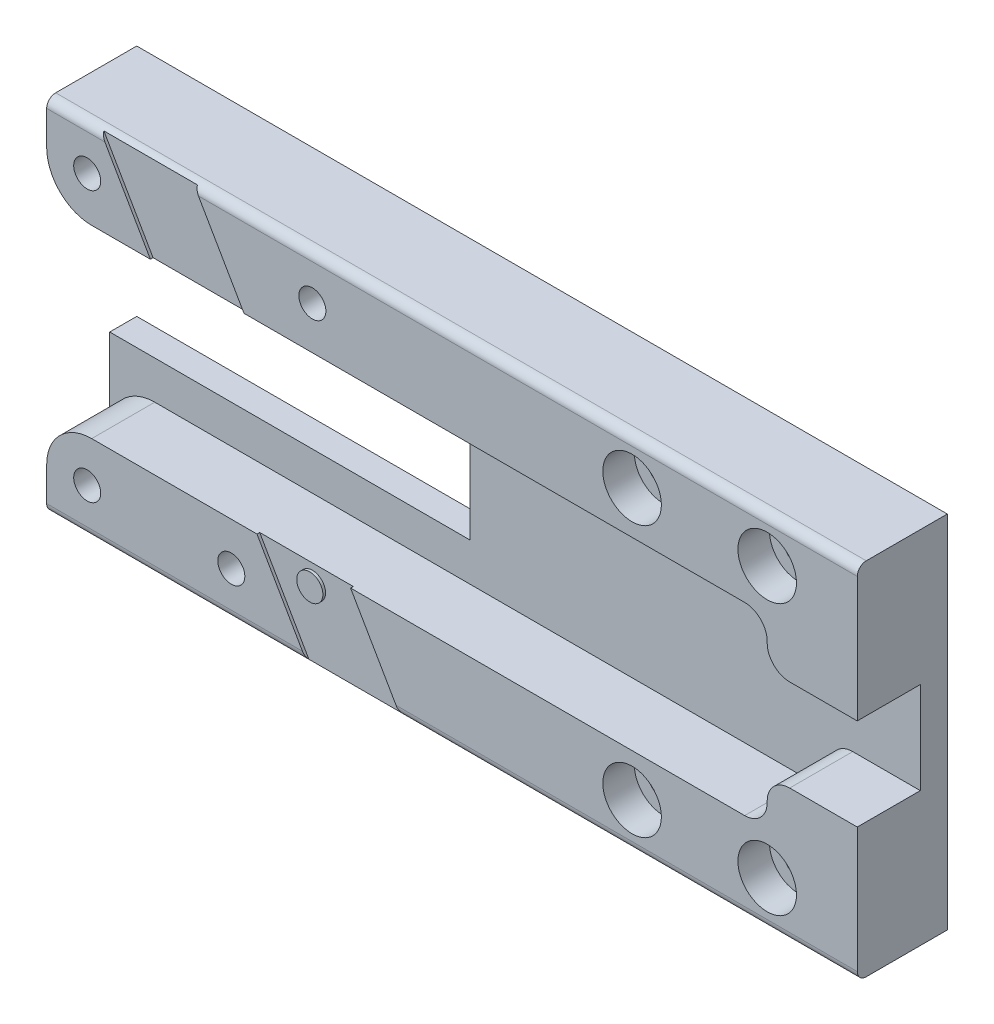
SolidWorks part; units mm, degrees
ref_plane "前视基准面" through (0, 0, 0) normal (0, 0, 1) x (1, 0, 0)
ref_plane "上视基准面" through (0, 0, 0) normal (0, 1, 0) x (1, 0, 0)
ref_plane "右视基准面" through (0, 0, 0) normal (1, 0, 0) x (0, 0, -1)
sketch "草图1" plane through (0, 0, 0) normal (0, 0, 1) x (1, 0, 0)
  line L1 (127.5, -40) -> (-127.5, -40)
  line L2 (127.5, -40) -> (127.5, 40)
  line L3 (127.5, 40) -> (-127.5, 40)
  line L4 (-127.5, -40) -> (-127.5, 40)
  line L5 (127.5, -40) -> (-127.5, 40) construction
  line L6 (127.5, 40) -> (-127.5, -40) construction
  point P0 (0, 0)
  dimension "D1" = 80
  dimension "D2" = 255
extrude "凸台-拉伸1" add sketch "草图1" along normal blind 5
sketch "草图2" plane through (0, 0, 5) normal (0, 0, 1) x (1, 0, 0)
  line L0 (-127.5, 40) -> (-127.5, -40) construction
  circle A0 centre (-107.5, 0) radius 5
  dimension "D1" = 10
  dimension "D2" = 20
extrude "切除-拉伸1" cut sketch "草图2" against normal blind 5
sketch "草图3" plane through (0, 0, 5) normal (0, 0, 1) x (1, 0, 0)
  circle A0 centre (-45, 0) radius 4
  dimension "D2" = 8
extrude "切除-拉伸2" cut sketch "草图3" against normal blind 10
sketch "草图4" plane through (0, 0, 5) normal (0, 0, 1) x (1, 0, 0)
  line L1 (2.5, -10) -> (-47.5, -10)
  line L2 (2.5, -10) -> (2.5, 10)
  line L3 (2.5, 10) -> (-47.5, 10)
  line L4 (-47.5, -10) -> (-47.5, 10)
  line L5 (2.5, -10) -> (-47.5, 10) construction
  line L6 (2.5, 10) -> (-47.5, -10) construction
  line L7 (-127.5, 40) -> (-127.5, -40) construction
  point P0 (-22.5, 0)
  dimension "D1" = 130
  dimension "D2" = 20
  dimension "D3" = 50
extrude "凸台-拉伸2" add sketch "草图4" along normal blind 10
sketch "草图5" plane through (0, 0, 5) normal (0, 0, 1) x (1, 0, 0)
  line L1 (-127.5, 40) -> (-127.5, -40) construction
  circle A0 centre (70, 0) radius 15
  dimension "D1" = 30
  dimension "D2" = 197.5
extrude "切除-拉伸3" cut sketch "草图5" against normal blind 10
sketch "草图6" plane through (0, 0, 0) normal (0, 0, -1) x (-1, 0, 0)
  circle A0 centre (107.5, 0) radius 7
  dimension "D1" = 14
extrude "凸台-拉伸3" add sketch "草图6" against normal blind 15
hole_wizard "M6 螺纹孔1" positions "草图8" profile "草图9" tap size "M6" standard "GB" end condition through all
sketch "草图8" plane through (0, 0, 15) normal (0, 0, 1) x (1, 0, 0)
  point P0 (-107.5, 0)
sketch "草图9" plane through (-107.5, 0, 15) normal (1, 0, 0) x (0, -1, 0)
  line L0 (0, 0) -> (0, 15)
  line L1 (0, 15) -> (2.5, 15)
  line L2 (2.5, 15) -> (2.5, 0)
  line L5 (2.5, 0) -> (0, 0)
  line L11 (0, -6.35) -> (0, 107.95) construction
  dimension "通孔螺纹孔钻头直径" = 5
  dimension "通孔螺纹孔钻头深度" = 15
cosmetic thread "孔螺蚊线1" parameters "D2"=6
sketch "草图10" plane through (0, 0, 15) normal (0, 0, 1) x (1, 0, 0)
  line L0 (-47.5, 0) -> (2.5, 0) construction
  line L1 (-47.5, 10) -> (-47.5, -10) construction
  line L2 (2.5, -10) -> (2.5, 10) construction
  line L3 (-47.5, 5.1) -> (2.5, 5.1)
  line L4 (-47.5, -5.1) -> (2.5, -5.1)
  arc A0 (-47.5, 5.1) -> (-47.5, -5.1) centre (-47.5, 0) ccw
  arc A1 (2.5, -5.1) -> (2.5, 5.1) centre (2.5, 0) ccw
  point P6 (-22.5, 0)
  dimension "D1" = 5.1
extrude "切除-拉伸4" cut sketch "草图10" against normal blind 7
hole_wizard "M4 螺纹孔1" positions "草图11" profile "草图12" tap size "M4" standard "GB" end condition through all
sketch "草图11" plane through (0, 0, 0) normal (0, 0, -1) x (-1, 0, 0)
  point P0 (-39.75, -26.5)
  point P3 (-39.75, -1.5)
  point P6 (-109.9401, -26.5)
  point P8 (-100.25, -1.5)
sketch "草图12" plane through (39.75, -26.5, 0) normal (1, 0, 0) x (0, 1, 0)
  line L0 (0, 0) -> (0, 15)
  line L1 (0, 15) -> (1.65, 15)
  line L2 (1.65, 15) -> (1.65, 0)
  line L5 (1.65, 0) -> (0, 0)
  line L11 (0, -6.35) -> (0, 107.95) construction
  dimension "通孔螺纹孔钻头直径" = 3.3
  dimension "通孔螺纹孔钻头深度" = 15
cosmetic thread "孔螺蚊线2" parameters "D2"=4
cosmetic thread "孔螺蚊线3" parameters "D2"=4
cosmetic thread "孔螺蚊线4" parameters "D2"=4
cosmetic thread "孔螺蚊线5" parameters "D2"=4
fillet "圆角1" radius 10 2 edges at (-127.5, -40, 2.5) (-127.5, 40, 2.5)
sketch "草图13" plane through (0, 0, 5) normal (0, 0, 1) x (1, 0, 0)
  circle A0 centre (-45, 0) radius 6.9694
extrude "凸台-拉伸5" add sketch "草图13" against normal blind 5
sketch "草图14" plane through (0, -40, 0) normal (0, -1, 0) x (1, 0, 0)
  line L1 (127.5, 0) -> (122.5, 0)
  line L2 (127.5, 0) -> (127.5, -75)
  line L3 (127.5, -75) -> (122.5, -75)
  line L4 (122.5, 0) -> (122.5, -75)
  dimension "D1" = 5
  dimension "D2" = 75
extrude "凸台-拉伸6" add sketch "草图14" against normal up to surface (80 mm away) up to face at (5, 40, 2.5)
sketch "草图15" plane through (0, -40, 0) normal (0, -1, 0) x (1, 0, 0)
  line L1 (122.5, -75) -> (102.5, -75)
  line L2 (122.5, -75) -> (122.5, -70)
  line L3 (122.5, -70) -> (102.5, -70)
  line L4 (102.5, -75) -> (102.5, -70)
  dimension "D1" = 5
  dimension "D2" = 20
extrude "凸台-拉伸7" add sketch "草图15" against normal up to surface (80 mm away) up to face at (44.1667, 40, -23.3333)
sketch "草图16" plane through (0, -40, 0) normal (0, -1, 0) x (1, 0, 0)
  line L0 (-32.5, 5) -> (-32.5, 0)
  line L1 (-117.5, 5) -> (127.5, 5) construction
  line L2 (-117.5, 0) -> (122.5, 0) construction
  line L3 (-32.5, 0) -> (102.5, -75)
  line L4 (102.5, -75) -> (127.5, -75)
  line L5 (127.5, -75) -> (127.5, 5)
  line L6 (127.5, 5) -> (-32.5, 5)
  dimension "D1" = 160
extrude "凸台-拉伸8" add sketch "草图16" against normal blind 5
mirror "镜向1" about plane through (0, 0, 0) normal (0, 1, 0) of "凸台-拉伸8"
sketch "草图17" plane through (0, 0, -75) normal (0, 0, -1) x (-1, 0, 0)
  circle A0 centre (-114.5, -15) radius 3
  circle A1 centre (-114.5, 15) radius 3
  dimension "D1" = 6
extrude "切除-拉伸5" cut sketch "草图17" against normal blind 5
fillet "圆角2" radius 1 20 edges at (-124.5711, 37.0711, 5) (-124.5711, 37.0711, 0) (-127.5, 0, 0) (-127.5, 0, 5) (-124.5711, -37.0711, 5) (-124.5711, -37.0711, 0) (5, 40, 5) (-75, 40, 0) (35, 40, -37.5) (115, 40, -75) (127.5, 0, -75) (127.5, 0, 5) (127.5, 40, -35) (5, -40, 5) (127.5, -40, -35) (115, -40, -75) (35, -40, -37.5) (-75, -40, 0) (35, -35, -37.5) (35, 35, -37.5)
fillet "圆角3" [suppressed] radius 1
sketch "草图18" plane through (0, 0, 5) normal (0, 0, 1) x (1, 0, 0)
  line L1 (154.807, -67.1452) -> (-154.807, -67.1452)
  line L2 (154.807, -67.1452) -> (154.807, 67.1452)
  line L3 (154.807, 67.1452) -> (-154.807, 67.1452)
  line L4 (-154.807, -67.1452) -> (-154.807, 67.1452)
  line L5 (154.807, -67.1452) -> (-154.807, 67.1452) construction
  line L6 (154.807, 67.1452) -> (-154.807, -67.1452) construction
  point P0 (0, 0)
extrude "切除-拉伸6" cut sketch "草图18" against normal through all
sketch "草图19" plane through (0, 0, 15) normal (0, 0, 1) x (1, 0, 0)
  circle A2 centre (-107.5, 0) radius 17
  circle A3 centre (-107.5, 0) radius 17
  dimension "D1" = 10
extrude "切除-拉伸7" cut sketch "草图19" against normal through all
sketch "草图20" plane through (2.5, 0, 0) normal (1, 0, 0) x (0, 0, -1)
  line L1 (-15, 10) -> (-5, 10)
  line L2 (-15, 10) -> (-15, 20)
  line L3 (-15, 20) -> (-5, 20)
  line L4 (-5, 10) -> (-5, 20)
  dimension "D1" = 10
extrude "凸台-拉伸9" add sketch "草图20" against normal up to surface (50 mm away) up to face at (-47.5, 0, 10.75)
mirror "镜向2" about plane through (0, 0, 0) normal (0, 1, 0) of "凸台-拉伸9"
sketch "草图21" plane through (0, 0, 15) normal (0, 0, 1) x (1, 0, 0)
  line L0 (2.5, -5.1) -> (2.5, 5.1) construction
  line L4 (-7.5, -15) -> (-37.5, -15) construction
  line L5 (-7.5, -15) -> (-7.5, 15) construction
  line L6 (-7.5, 15) -> (-37.5, 15) construction
  line L7 (-37.5, -15) -> (-37.5, 15) construction
  line L8 (-7.5, -15) -> (-37.5, 15) construction
  line L9 (-7.5, 15) -> (-37.5, -15) construction
  circle A0 centre (-37.5, 15) radius 1.75 construction
  circle A1 centre (-22.5, 15) radius 1.75
  circle A2 centre (-7.5, 15) radius 1.75
  circle A3 centre (-7.5, -15) radius 1.75
  circle A4 centre (-22.5, -15) radius 1.75
  circle A5 centre (-37.5, -15) radius 1.75 construction
  point P6 (-22.5, 0)
  dimension "D3" = 3.5
  dimension "D1" = 30
  dimension "D2" = 30
  dimension "D4" = 10
extrude "切除-拉伸8" cut sketch "草图21" against normal through all
sketch "草图22" plane through (0, 0, 15) normal (0, 0, 1) x (1, 0, 0)
  circle A1 centre (-22.5, 15) radius 3.25
  circle A2 centre (-7.5, 15) radius 3.25
  circle A3 centre (-7.5, -15) radius 3.25
  circle A4 centre (-22.5, -15) radius 3.25
  dimension "D1" = 6.5
extrude "切除-拉伸9" cut sketch "草图22" against normal blind 3.5
fillet "圆角4" radius 1 2 edges at (-22.5, -20, 15) (-22.5, 20, 15)
sketch "草图23" plane through (-47.5, 0, 0) normal (-1, 0, 0) x (0, 0, 1)
  line L8 (5, -20) -> (14, -20)
  line L9 (15, -19) -> (15, -5.1)
  line L10 (15, -5.1) -> (8, -5.1)
  line L11 (8, -5.1) -> (8, 5.1)
  line L12 (8, 5.1) -> (15, 5.1)
  line L14 (14, 20) -> (5, 20)
  line L15 (5, 20) -> (5, -20)
  line L16 (5, -20) -> (14, -20)
  line L18 (15, -5.1) -> (8, -5.1)
  line L19 (8, -5.1) -> (8, 5.1)
  line L20 (8, 5.1) -> (15, 5.1)
  line L22 (14, 20) -> (5, 20)
  line L23 (5, 20) -> (5, -20)
  line L24 (15, -19) -> (15, -5.1)
  line L25 (15, 5.1) -> (15, 19)
  line L26 (15, 5.1) -> (15, 19)
  arc A4 (14, -20) -> (15, -19) centre (14, -19) ccw
  arc A7 (15, 19) -> (14, 20) centre (14, 19) ccw
  arc A8 (14, -20) -> (15, -19) centre (14, -19) ccw
  arc A11 (15, 19) -> (14, 20) centre (14, 19) ccw
  dimension "D1" = 0
extrude "凸台-拉伸10" add sketch "草图23" along normal blind 40
sketch "草图24" plane through (0, 0, 15) normal (0, 0, 1) x (1, 0, 0)
  line L0 (-87.5, -5.1) -> (-87.5, 5.1) construction
  line L1 (-167.5, -10.25) -> (-7.5, -10.25)
  line L2 (-167.5, -10.25) -> (-167.5, 10.25)
  line L3 (-167.5, 10.25) -> (-7.5, 10.25)
  line L4 (-7.5, -10.25) -> (-7.5, 10.25)
  line L5 (-167.5, -10.25) -> (-7.5, 10.25) construction
  line L6 (-167.5, 10.25) -> (-7.5, -10.25) construction
  line L7 (2.5, -5.1) -> (2.5, 5.1) construction
  point P0 (-87.5, 0)
  dimension "D1" = 20.5
  dimension "D2" = 10
extrude "切除-拉伸10" cut sketch "草图24" against normal up to surface (7 mm away) up to face at (-42.5, 0, 8)
sketch "草图25" plane through (0, 0, 8) normal (0, 0, 1) x (1, 0, 0)
  line L0 (-87.5, -10.25) -> (-87.5, 10.25) construction
  line L1 (-127.5, -6) -> (-47.5, -6)
  line L2 (-127.5, -6) -> (-127.5, 6)
  line L3 (-127.5, 6) -> (-47.5, 6)
  line L4 (-47.5, -6) -> (-47.5, 6)
  line L5 (-127.5, -6) -> (-47.5, 6) construction
  line L6 (-127.5, 6) -> (-47.5, -6) construction
  point P0 (-87.5, 0)
  dimension "D1" = 12
  dimension "D2" = 80
extrude "切除-拉伸11" cut sketch "草图25" against normal through all
fillet "圆角5" radius 5 2 edges at (-87.5, -10.25, 11.5) (-87.5, 10.25, 11.5)
sketch "草图26" plane through (0, 0, 15) normal (0, 0, 1) x (1, 0, 0)
  line L0 (-58.5215, -20) -> (-81.6155, 20)
  line L1 (-59, -19.1711) -> (-81.5, 19.8) construction
  line L2 (-58.5215, -20) -> (-48.1292, -20)
  line L3 (-48.1292, -20) -> (-71.2232, 20)
  line L4 (-71.2232, 20) -> (-81.6155, 20)
  line L5 (-87.5, 20) -> (2.5, 20) construction
  line L6 (2.5, -20) -> (-87.5, -20) construction
  line L7 (-58.6077, -1.8506) -> (-61.1077, 2.4795) construction
extrude "切除-拉伸12" cut sketch "草图26" against normal blind 0.3
sketch "草图27" plane through (0, 0, 14.7) normal (0, 0, 1) x (1, 0, 0)
  circle A0 centre (-58.2859, -12.408) radius 1.45
  dimension "D1" = 2.9
extrude "凸台-拉伸11" add sketch "草图27" along normal blind 0.3
hole_wizard "Ø3.0mm 暗销孔1" positions "草图28" profile "草图29" hole size "Ø3.0" standard "GB" end condition through all
sketch "草图28" plane through (0, 0, 15) normal (0, 0, 1) x (1, 0, 0)
  point P0 (-83, 15)
  point P3 (-58, 15)
  point P12 (-67, -15)
  point P15 (-83, -15)
sketch "草图29" plane through (-83, 15, 15) normal (1, 0, 0) x (0, -1, 0)
  line L0 (0, 0) -> (0, 10)
  line L1 (0, 10) -> (1.5, 10)
  line L2 (1.5, 10) -> (1.5, 0)
  line L5 (1.5, 0) -> (0, 0)
  line L11 (0, -6.35) -> (0, 107.95) construction
  dimension "通孔孔直径" = 3
  dimension "通孔孔深度" = 10
fillet "圆角6" radius 2.5 4 edges at (-7.5, 10.25, 11.5) (-7.5, -10.25, 11.5) (-7.5, -5.1, 11.5) (-7.5, 5.1, 11.5)
